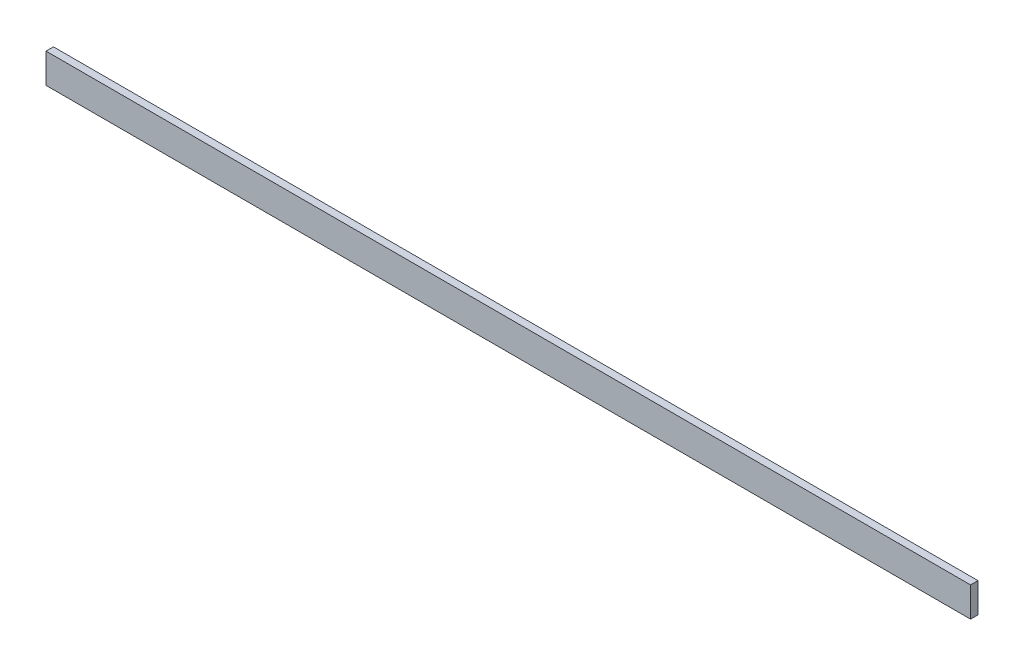
SolidWorks part; units mm, degrees
material "6061-T6 (SS)"
ref_plane "Front Plane" through (0, 0, 0) normal (0, 0, 1) x (1, 0, 0)
ref_plane "Top Plane" through (0, 0, 0) normal (0, 1, 0) x (1, 0, 0)
ref_plane "Right Plane" through (0, 0, 0) normal (1, 0, 0) x (0, 0, -1)
sketch "Sketch1" plane through (0, 0, 0) normal (0, 0, 1) x (1, 0, 0)
  line L0 (-316.1, 0) -> (-316.1, 289.475) construction
  line L1 (-316.1, 289.475) -> (-237.075, 289.475) construction
  line L2 (-158.05, 289.475) -> (-237.075, 289.475) construction
  line L3 (-158.05, 289.475) -> (-79.025, 289.475) construction
  line L4 (-79.025, 289.475) -> (0, 289.475) construction
  line L5 (0, 0) -> (0, 289.475) construction
  line L6 (-316.1, 0) -> (-316.1, 289.475) construction
  line L7 (-316.1, 289.475) -> (-237.075, 289.475) construction
  line L8 (-158.05, 289.475) -> (-237.075, 289.475) construction
  line L9 (-158.05, 289.475) -> (-79.025, 289.475) construction
  line L10 (-79.025, 289.475) -> (0, 289.475) construction
  line L11 (0, 0) -> (0, 289.475) construction
  line L12 (39.6875, -1.5875) -> (39.6875, 291.0625) construction
  line L13 (39.6875, 303.699) -> (-355.7875, 303.699)
  line L14 (39.6875, 303.699) -> (39.6875, 290.999)
  line L15 (39.6875, 290.999) -> (-355.7875, 290.999)
  line L16 (-158.05, 303.699) -> (-158.05, 290.999) construction
  line L18 (-355.7875, 303.699) -> (-355.7875, 290.999)
  dimension "D1" = 1.524
  dimension "D2" = 12.7
extrude "Boss-Extrude1" add sketch "Sketch1" along normal blind 3.175
equation "\"D2@Sketch1\"=\"Acc Lid Flange Width@FS2-EN-ACC-A-0003-V1, ACCUMULATOR CONTAINER.Assembly\""
equation "\"D1@Boss-Extrude1\"=\"acc lid flange thickness@FS2-EN-ACC-A-0003-V1, ACCUMULATOR CONTAINER.Assembly\""
